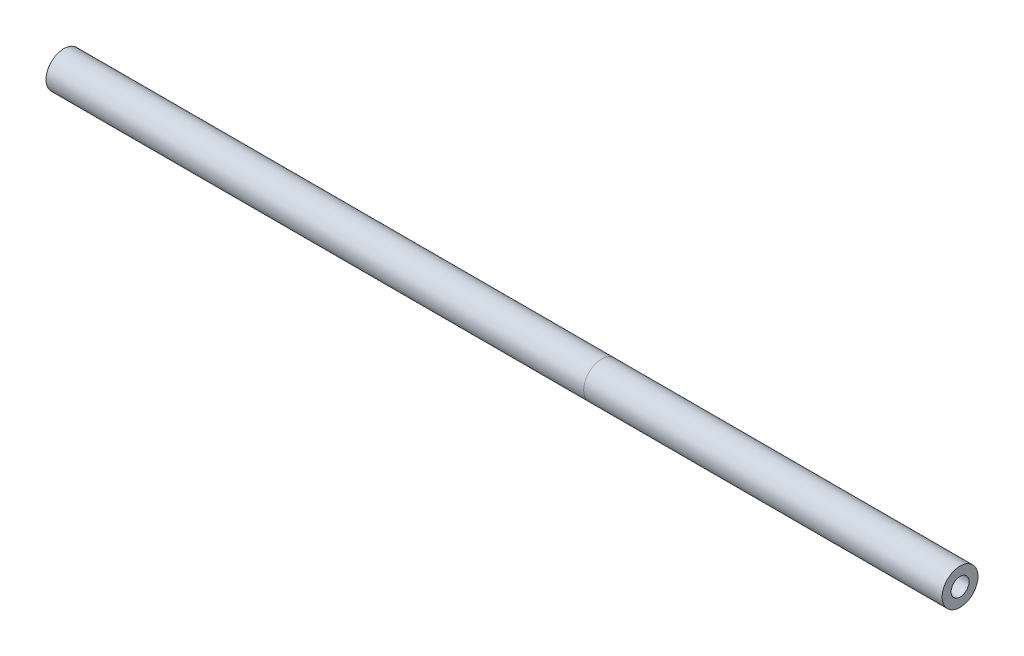
SolidWorks part; units mm, degrees
ref_plane "Front Plane" through (0, 0, 0) normal (0, 0, 1) x (1, 0, 0)
ref_plane "Top Plane" through (0, 0, 0) normal (0, 1, 0) x (1, 0, 0)
ref_plane "Right Plane" through (0, 0, 0) normal (1, 0, 0) x (0, 0, -1)
sketch "Sketch1" plane through (0, 0, 0) normal (0, 0, 1) x (1, 0, 0)
  line L0 (0, 0) -> (600, 0)
  line L1 (600, 0) -> (1000, 0)
  dimension "D1" = 600
  dimension "D2" = 400
other "Pipe 33.7 X 4.0(2)"
ref_plane "Plane2" through (0, 0, 0) normal (1, 0, 0) x (0, 1, 0)
sketch "Sketch12" plane through (0, 0, 0) normal (1, 0, 0) x (0, 1, 0)
  circle A0 centre (0, 0) radius 10
  circle A1 centre (0, 0) radius 20
  point P3 (0, 20)
  point P5 (-20, 0)
  point P6 (0, -20)
  point P7 (20, 0)
  point P8 (0, 0)
  dimension "In_dia" = 20
  dimension "Out_dia" = 40
